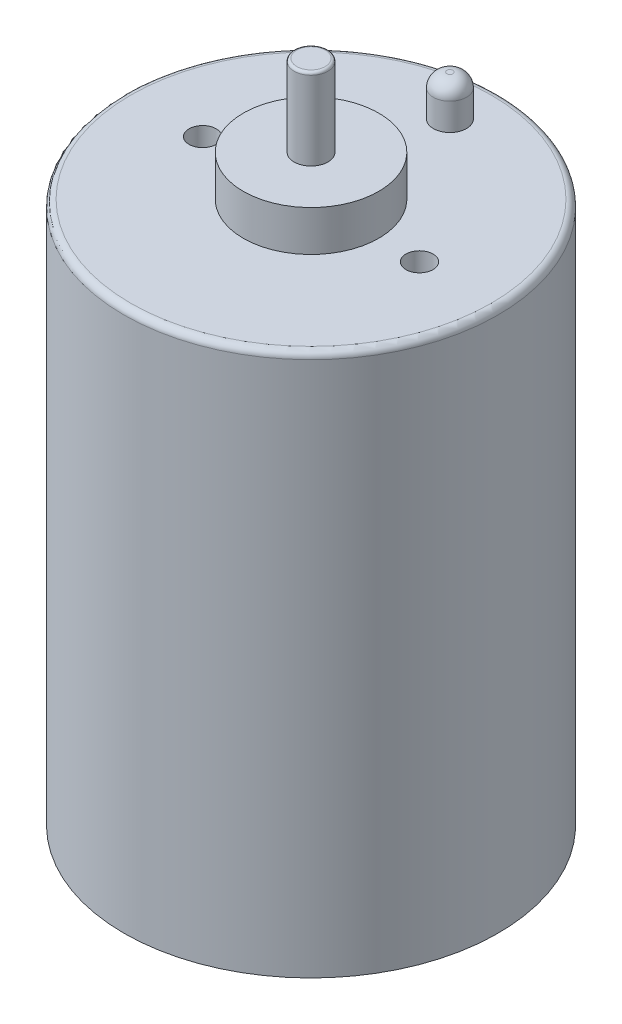
SolidWorks part; units mm, degrees
ref_plane "Front Plane" through (0, 0, 0) normal (0, 0, 1) x (1, 0, 0)
ref_plane "Top Plane" through (0, 0, 0) normal (0, 1, 0) x (1, 0, 0)
ref_plane "Right Plane" through (0, 0, 0) normal (1, 0, 0) x (0, 0, -1)
sketch "Sketch1" plane through (0, 0, 0) normal (0, 1, 0) x (1, 0, 0)
  circle A0 centre (0, 0) radius 13.8
  dimension "D1" = 27.6
extrude "Boss-Extrude1" add sketch "Sketch1" along normal blind 40
sketch "Sketch2" plane through (0, 40, 0) normal (0, 1, 0) x (1, 0, 0)
  circle A0 centre (0, 0) radius 5
  dimension "D1" = 10
extrude "Boss-Extrude2" add sketch "Sketch2" along normal blind 3
sketch "Sketch3" plane through (0, 40, 0) normal (0, 1, 0) x (1, 0, 0)
  line L0 (8, 0) -> (-8, 0) construction
  line L1 (-8, 0) -> (0, 10.247) construction
  line L2 (0, 10.247) -> (8, 0) construction
  circle A0 centre (-8, 0) radius 1
  circle A1 centre (8, 0) radius 1
  point P4 (0, 0)
  dimension "D1" = 2
  dimension "D2" = 16
  dimension "D3" = 13
extrude "Cut-Extrude1" cut sketch "Sketch3" against normal blind 3
sketch "Sketch4" plane through (0, 40, 0) normal (0, 1, 0) x (1, 0, 0)
  line L0 (-8, 0) -> (0, 10.247) construction
  line L1 (0, 10.247) -> (8, 0) construction
  circle A0 centre (0, 10.247) radius 1.225
  dimension "D2" = 2.45
  dimension "D1" = 13
extrude "Boss-Extrude3" add sketch "Sketch4" along normal blind 3
fillet "Fillet1" radius 1 1 edges at (0, 43, -9.022)
fillet "Fillet2" radius 0.5 1 edges at (0, 40, 13.8)
sketch "Sketch5" plane through (0, 43, 0) normal (0, 1, 0) x (1, 0, 0)
  circle A0 centre (0, 0) radius 1.25
  dimension "D1" = 2.5
extrude "Boss-Extrude4" add sketch "Sketch5" along normal blind 6
fillet "Fillet3" radius 0.2 1 edges at (0, 49, 1.25)
